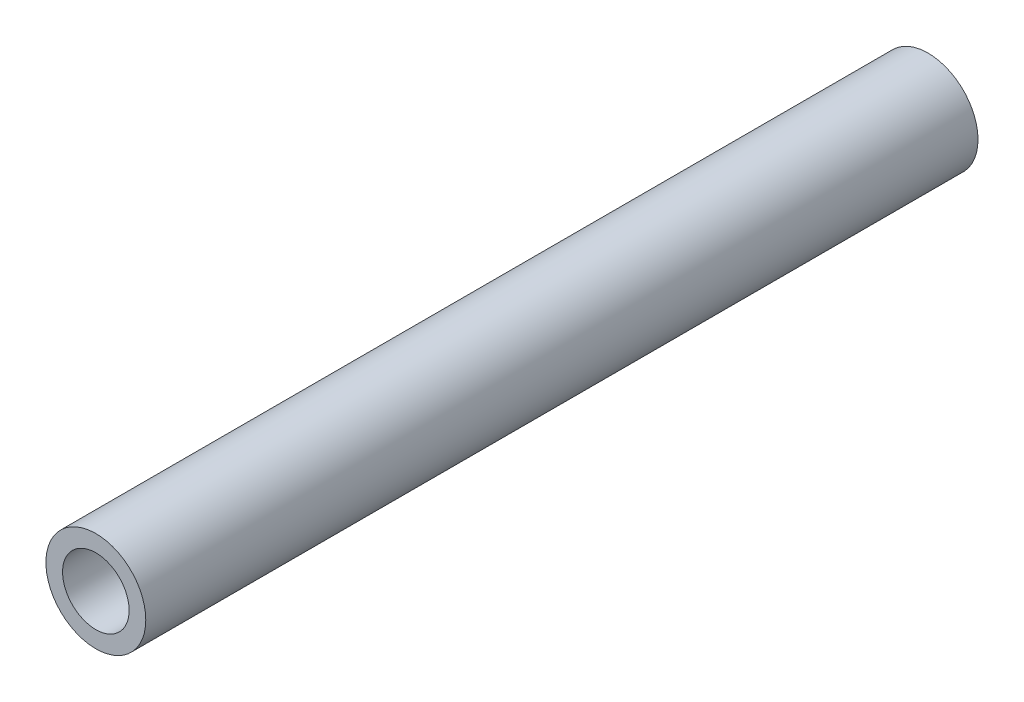
SolidWorks part; units mm, degrees
material "PVC Rigid"
ref_plane "Front Plane" through (0, 0, 0) normal (0, 0, 1) x (1, 0, 0)
ref_plane "Top Plane" through (0, 0, 0) normal (0, 1, 0) x (1, 0, 0)
ref_plane "Right Plane" through (0, 0, 0) normal (1, 0, 0) x (0, 0, -1)
sketch "Sketch1" plane through (0, 0, 0) normal (0, 0, 1) x (1, 0, 0)
  circle A0 centre (0, 0) radius 7.62
  circle A2 centre (0, 0) radius 5.08
  dimension "D1" = 15.24
  dimension "D2" = 10.16
extrude "Boss-Extrude1" add sketch "Sketch1" along normal blind 127
